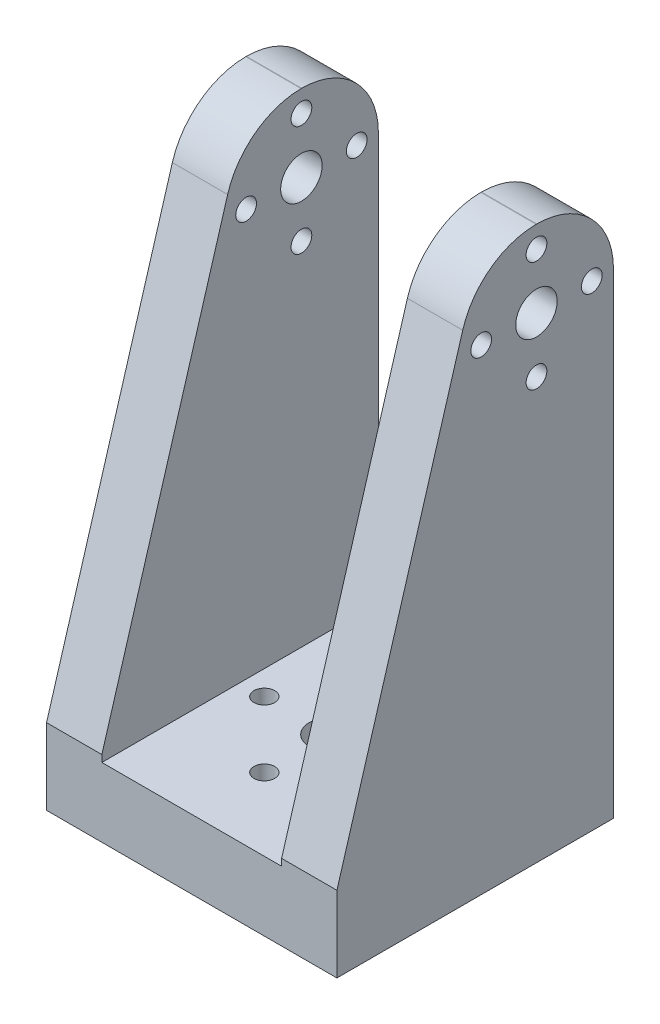
SolidWorks part; units mm, degrees
material "ABS"
ref_plane "Płaszczyzna przednia" through (0, 0, 0) normal (0, 0, 1) x (1, 0, 0)
ref_plane "Płaszczyzna górna" through (0, 0, 0) normal (0, 1, 0) x (1, 0, 0)
ref_plane "Płaszczyzna prawa" through (0, 0, 0) normal (1, 0, 0) x (0, 0, -1)
sketch "Szkic1" plane through (0, 0, 0) normal (0, 0, 1) x (1, 0, 0)
  line L0 (0, 0) -> (0, 80) construction
  line L1 (13, 10) -> (-13, 10)
  line L2 (-13, 10) -> (-13, 80)
  line L3 (-13, 80) -> (-21, 80)
  line L4 (-21, 80) -> (-21, 0)
  line L5 (-21, 0) -> (21, 0)
  line L6 (13, 80) -> (21, 80)
  line L7 (21, 80) -> (21, 0)
  line L8 (13, 10) -> (13, 80)
  point P12 (0, 10)
  dimension "D1" = 80
  dimension "D2" = 10
  dimension "D3" = 13
  dimension "D4" = 21
extrude "Dodanie-wyciągnięcie1" add sketch "Szkic1" along normal blind 40
sketch "Szkic2" plane through (21, 0, 0) normal (1, 0, 0) x (0, 0, -1)
  line L0 (0, 10.9869) -> (-40, 10.9869)
  line L1 (0, 0) -> (0, 80) construction
  line L2 (-40, 0) -> (-40, 80) construction
  line L3 (-40, 10.9869) -> (-21.8049, 72.0457)
  line L4 (-0.0004, 68.866) -> (0, 10.9869)
  circle A0 centre (-11.1345, 68.866) radius 3
  arc A1 (-0.0004, 68.866) -> (-21.8049, 72.0457) centre (-11.1345, 68.866) ccw
  line M2 (0, 0) -> (0, 80)
  line M3 (0, 80) -> (-40, 80)
  line M4 (-40, 80) -> (-40, 0)
  dimension "D1" = 22.2682
  dimension "D2" = 6
extrude "Wytnij-wyciągnięcie1" cut sketch "Szkic2" against normal through all contours A1 L3 M3 M4 | A1 L4 M2 M3 | A0
sketch "Szkic3" plane through (0, 10, 0) normal (0, 1, 0) x (1, 0, 0)
  line L0 (0, 0) -> (0, -40) construction
  line L1 (13, -40) -> (-13, -40) construction
  circle A0 centre (0, -20) radius 3
  circle A1 centre (0, -10.5) radius 1.5
  circle A2 centre (9.5, -20) radius 1.5
  circle A3 centre (0, -29.5) radius 1.5
  circle A4 centre (-9.5, -20) radius 1.5
  point P18 (0, -20)
  dimension "D1" = 3
  dimension "D2" = 6
  dimension "D3" = 9.5
  dimension "D4" = 4
extrude "Wytnij-wyciągnięcie2" cut sketch "Szkic3" against normal through all
sketch "Szkic4" plane through (-21, 0, 0) normal (-1, 0, 0) x (0, 0, 1)
  line L0 (11.1345, 68.866) -> (-10.5554, 68.866) construction
  circle A0 centre (3.1345, 68.866) radius 1.5
  circle A1 centre (11.1345, 76.866) radius 1.5
  circle A2 centre (19.1345, 68.866) radius 1.5
  circle A3 centre (11.1345, 60.866) radius 1.5
  point P2 (11.1345, 68.866)
  point P15 (11.1345, 68.866)
  dimension "D1" = 8
  dimension "D3" = 3
  dimension "D2" = 4
extrude "Wytnij-wyciągnięcie3" cut sketch "Szkic4" against normal through all
